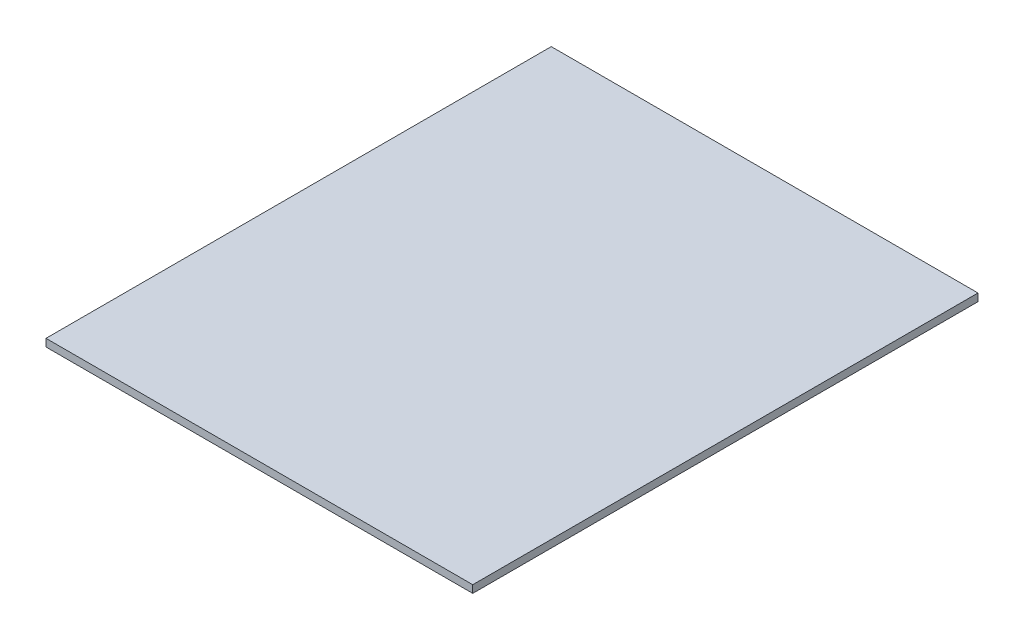
SolidWorks part; units mm, degrees
ref_plane "Front Plane" through (0, 0, 0) normal (0, 0, 1) x (1, 0, 0)
ref_plane "Top Plane" through (0, 0, 0) normal (0, 1, 0) x (1, 0, 0)
ref_plane "Right Plane" through (0, 0, 0) normal (1, 0, 0) x (0, 0, -1)
sketch "Sketch2" plane through (0, 0, 0) normal (0, 1, 0) x (1, 0, 0)
  line L1 (0, 0) -> (565.88, 0)
  line L2 (0, 0) -> (0, 670)
  line L3 (0, 670) -> (565.88, 670)
  line L4 (565.88, 0) -> (565.88, 670)
  dimension "D1" = 565.88
  dimension "D2" = 670
extrude "Extrude1" add sketch "Sketch2" along normal blind 10
